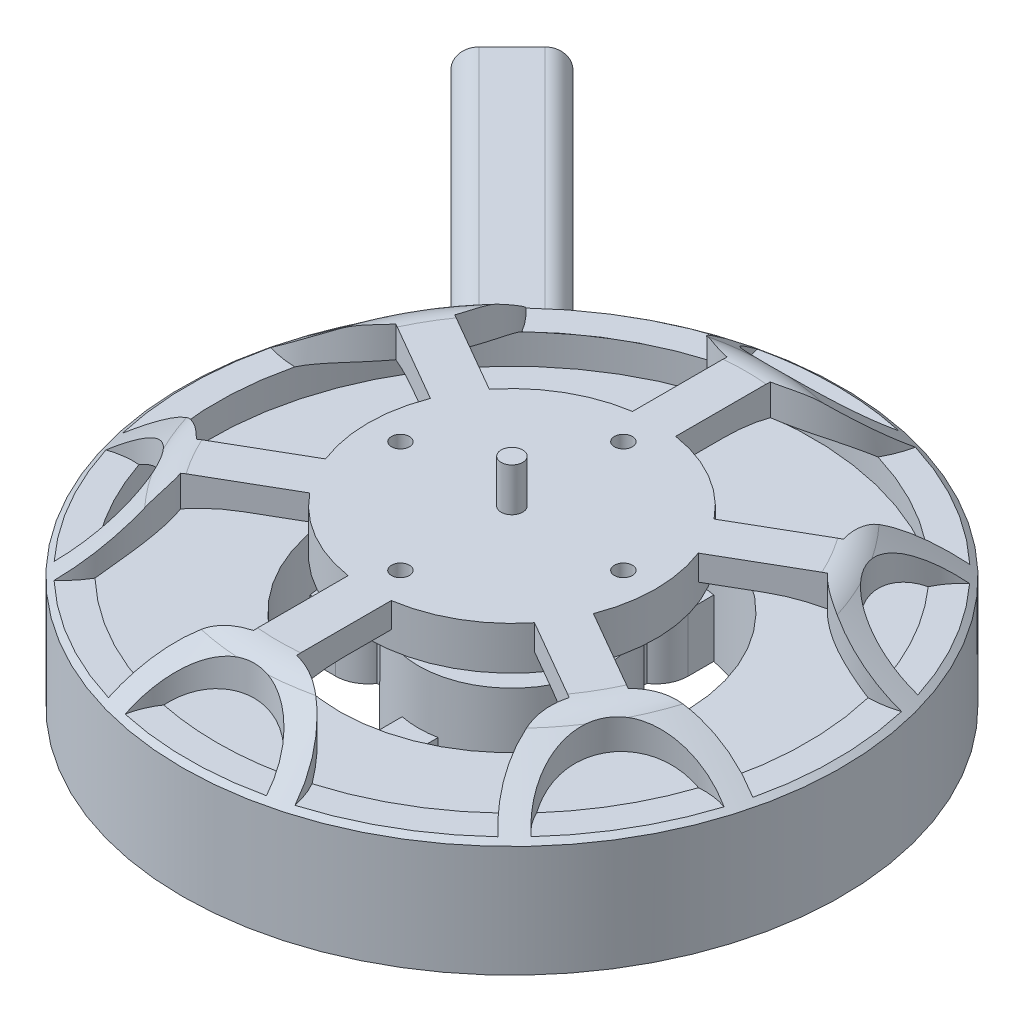
SolidWorks part; units mm, degrees
ref_plane "Front Plane" through (0, 0, 0) normal (0, 0, 1) x (1, 0, 0)
ref_plane "Top Plane" through (0, 0, 0) normal (0, 1, 0) x (1, 0, 0)
ref_plane "Right Plane" through (0, 0, 0) normal (1, 0, 0) x (0, 0, -1)
ref_axis "Axis1" through (0, 40.089, 0) along (0, -1, 0)
sketch "Sketch1" plane through (0, 0, 0) normal (0, 0, 1) x (1, 0, 0)
  line L0 (0, 0) -> (9.65, 0)
  line L1 (9.65, 0) -> (9.65, 3.93)
  line L2 (9.65, 3.93) -> (27.5, 3.93)
  line L3 (27.5, 3.93) -> (45.83, 8.08)
  line L4 (45.83, 8.08) -> (45.83, 23.58)
  line L5 (45.83, 23.58) -> (36.1322, 30.9557)
  line L6 (32.5, 32.18) -> (1.5, 32.18)
  line L7 (1.5, 32.18) -> (1.5, 38.18)
  line L8 (1.5, 38.18) -> (0, 38.18)
  line L9 (0, 38.18) -> (0, 0) construction
  line L10 (0, 0) -> (0, 38.18)
  arc A0 (36.1322, 30.9557) -> (32.5, 32.18) centre (32.5, 26.18) ccw
  dimension "D10" = 6
  dimension "D1" = 3
  dimension "D2" = 6
  dimension "D3" = 28.25
  dimension "D4" = 3.93
  dimension "D5" = 19.3
  dimension "D6" = 4.15
  dimension "D7" = 91.66
  dimension "D8" = 55
  dimension "D9" = 65
  dimension "D11" = 15.5
revolve "Revolve1" add sketch "Sketch1" angle 360 about L9
sketch "Sketch2" plane through (0, 3.93, 0) normal (0, -1, 0) x (1, 0, 0)
  line L0 (0, 0) -> (0, 27.5) construction
  line L1 (2.5, 12.7574) -> (2.5, 16.2583)
  line L2 (4.5, 20) -> (4.5, 23.5744)
  line L3 (0, 0) -> (16.9706, 16.9706) construction
  line L4 (20, 4.5) -> (23.5744, 4.5)
  line L5 (12.7574, 2.5) -> (16.2583, 2.5)
  line L6 (20, -4.5) -> (23.5744, -4.5)
  line L7 (4.5, -20) -> (4.5, -23.5744)
  line L8 (2.5, -12.7574) -> (2.5, -16.2583)
  line L9 (12.7574, -2.5) -> (16.2583, -2.5)
  line L10 (-4.5, -20) -> (-4.5, -23.5744)
  line L11 (-20, -4.5) -> (-23.5744, -4.5)
  line L12 (-12.7574, -2.5) -> (-16.2583, -2.5)
  line L13 (-2.5, -12.7574) -> (-2.5, -16.2583)
  line L14 (-20, 4.5) -> (-23.5744, 4.5)
  line L15 (-4.5, 20) -> (-4.5, 23.5744)
  line L16 (-2.5, 12.7574) -> (-2.5, 16.2583)
  line L17 (-12.7574, 2.5) -> (-16.2583, 2.5)
  arc A0 (4.5, 23.5744) -> (23.5744, 4.5) centre (0, 0) cw
  arc A1 (4.5, 20) -> (2.5, 16.2583) centre (0, 20) cw
  arc A2 (2.5, 12.7574) -> (12.7574, 2.5) centre (0, 0) cw
  circle A3 centre (0, 0) radius 27.5 construction
  arc A4 (20, 4.5) -> (16.2583, 2.5) centre (20, 0) ccw
  arc A5 (20, -4.5) -> (16.2583, -2.5) centre (20, 0) cw
  arc A6 (23.5744, -4.5) -> (4.5, -23.5744) centre (0, 0) cw
  arc A7 (4.5, -20) -> (2.5, -16.2583) centre (0, -20) ccw
  arc A8 (12.7574, -2.5) -> (2.5, -12.7574) centre (0, 0) cw
  arc A9 (-4.5, -20) -> (-2.5, -16.2583) centre (0, -20) cw
  arc A10 (-4.5, -23.5744) -> (-23.5744, -4.5) centre (0, 0) cw
  arc A11 (-20, -4.5) -> (-16.2583, -2.5) centre (-20, 0) ccw
  arc A12 (-2.5, -12.7574) -> (-12.7574, -2.5) centre (0, 0) cw
  arc A13 (-20, 4.5) -> (-16.2583, 2.5) centre (-20, 0) cw
  arc A14 (-23.5744, 4.5) -> (-4.5, 23.5744) centre (0, 0) cw
  arc A15 (-4.5, 20) -> (-2.5, 16.2583) centre (0, 20) ccw
  arc A16 (-12.7574, 2.5) -> (-2.5, 12.7574) centre (0, 0) cw
  point P4 (0, 20)
  point P51 (0, 0)
  dimension "D2" = 13
  dimension "D5" = 24
  dimension "D1" = 20
  dimension "D3" = 5
  dimension "D4" = 9
  dimension "D6" = 45
  dimension "D7" = 4
hole_wizard "M4x0.7 Tapped Hole1" positions "3DSketch1" profile "Sketch4" tap size "M4x0.7" standard "ANSI Metric"
sketch3d "3DSketch1"
  point P0 (-20, 3.93, 0)
  point P3 (0, 3.93, 20)
  point P6 (20, 3.93, 0)
  point P9 (0, 3.93, -20)
sketch "Sketch4" plane through (-20, 3.93, 0) normal (1, 0, 0) x (0, 0, -1)
  line L0 (0, 0) -> (0, 8.9914)
  line L1 (0, 8.9914) -> (1.65, 8)
  line L2 (1.65, 8) -> (1.65, 0)
  line L5 (1.65, 0) -> (0, 0)
  line L10 (0, 8.9914) -> (-1.65, 8) construction
  line L11 (0, -6.35) -> (0, 107.95) construction
  dimension "Tap Drill Dia." = 3.3
  dimension "Tap Drill Depth" = 8
  dimension "Drill Angle" = 118
cosmetic thread "Hole Thread1" parameters "D1"=7.874, "D2"=4
cosmetic thread "Hole Thread2" parameters "D1"=7.874, "D2"=4
cosmetic thread "Hole Thread3" parameters "D1"=7.874, "D2"=4
cosmetic thread "Hole Thread4" parameters "D1"=7.874, "D2"=4
extrude "Cut-Extrude1" cut sketch "Sketch2" against normal blind 8
sketch "Sketch5" plane through (0, 0, 0) normal (0, 0, 1) x (1, 0, 0)
  line L0 (24, 19.43) -> (41.83, 19.43)
  line L1 (-27.5, 3.93) -> (27.5, 3.93) construction
  line L2 (41.83, 19.43) -> (41.83, 23.58)
  line L3 (45.83, 8.08) -> (45.83, 23.58) construction
  line L4 (10, 19.43) -> (13, 19.43)
  line L5 (13, 19.43) -> (13, 11.93)
  line L6 (13, 11.93) -> (24, 11.93)
  line L7 (24, 11.93) -> (24, 19.43)
  line L8 (0, 40.089) -> (0, -1.909) construction
  line L9 (4.5, 11.93) -> (23.5744, 11.93) construction
  line L10 (45.83, 23.58) -> (-45.83, 23.58) construction
  line L11 (20, 28.68) -> (26.6996, 28.68)
  line L12 (32.5, 32.18) -> (-32.5, 32.18) construction
  line L13 (41.83, 23.58) -> (45.83, 20.5378) construction
  line L14 (45.83, 23.58) -> (36.1322, 30.9557) construction
  line L15 (20, 28.68) -> (20, 26.18)
  line L16 (20, 26.18) -> (10, 26.18)
  line L17 (10, 26.18) -> (10, 19.43)
  arc A0 (26.6996, 28.68) -> (41.83, 23.58) centre (26.6996, 3.6861) cw
  dimension "D1" = 15.5
  dimension "D2" = 4
  dimension "D3" = 13
  dimension "D4" = 24
  dimension "D5" = 3.5
  dimension "D6" = 20
  dimension "D7" = 6
  dimension "D8" = 10
revolve "Cut-Revolve3" cut sketch "Sketch5" angle 360 about axis through (0, 40.089, 0) along (0, -1, 0)
sketch "Sketch6" plane through (0, 0, 0) normal (0, 1, 0) x (1, 0, 0)
  line L0 (-3, 19.7737) -> (-3, 32.9241)
  line L1 (3, 19.7737) -> (3, 32.9241)
  line L2 (-3, 19.7737) -> (3, 19.7737) construction
  line L3 (0, 45.83) -> (0, 35.83) construction
  line L4 (15.6245, 12.4849) -> (27.0131, 19.0601)
  line L5 (18.6245, 7.2888) -> (30.0131, 13.864)
  line L6 (15.6245, 12.4849) -> (18.6245, 7.2888) construction
  line L7 (39.6899, 22.915) -> (31.0297, 17.915) construction
  line L8 (18.6245, -7.2888) -> (30.0131, -13.864)
  line L9 (15.6245, -12.4849) -> (27.0131, -19.0601)
  line L10 (18.6245, -7.2888) -> (15.6245, -12.4849) construction
  line L11 (39.6899, -22.915) -> (31.0297, -17.915) construction
  line L12 (3, -19.7737) -> (3, -32.9241)
  line L13 (-3, -19.7737) -> (-3, -32.9241)
  line L14 (3, -19.7737) -> (-3, -19.7737) construction
  line L15 (0, -45.83) -> (0, -35.83) construction
  line L16 (-15.6245, -12.4849) -> (-27.0131, -19.0601)
  line L17 (-18.6245, -7.2888) -> (-30.0131, -13.864)
  line L18 (-15.6245, -12.4849) -> (-18.6245, -7.2888) construction
  line L19 (-39.6899, -22.915) -> (-31.0297, -17.915) construction
  line L20 (-18.6245, 7.2888) -> (-30.0131, 13.864)
  line L21 (-15.6245, 12.4849) -> (-27.0131, 19.0601)
  line L22 (-18.6245, 7.2888) -> (-15.6245, 12.4849) construction
  line L23 (-39.6899, 22.915) -> (-31.0297, 17.915) construction
  line L24 (0, 15.5) -> (15.5, 0) construction
  line L25 (15.5, 0) -> (0, -15.5) construction
  line L26 (0, -15.5) -> (-15.5, 0) construction
  line L27 (-15.5, 0) -> (0, 15.5) construction
  arc A1 (-9.9403, 44.739) -> (9.9403, 44.739) centre (0, 45.83) ccw
  circle A2 centre (0, 0) radius 45.83 construction
  arc A3 (-13.1108, 43.9146) -> (-3, 32.9241) centre (0, 45.83) ccw
  arc A4 (13.1108, 43.9146) -> (3, 32.9241) centre (0, 45.83) cw
  arc A5 (-13.1108, 43.9146) -> (-9.9403, 44.739) centre (0, 0) cw
  arc A6 (9.9403, 44.739) -> (13.1108, 43.9146) centre (0, 0) cw
  arc A7 (33.775, 30.9781) -> (43.7153, 13.7609) centre (39.6899, 22.915) ccw
  arc A8 (31.4758, 33.3116) -> (27.0131, 19.0601) centre (39.6899, 22.915) ccw
  arc A9 (44.5866, 10.603) -> (30.0131, 13.864) centre (39.6899, 22.915) cw
  arc A10 (31.4758, 33.3116) -> (33.775, 30.9781) centre (0, 0) cw
  arc A11 (43.7153, 13.7609) -> (44.5866, 10.603) centre (0, 0) cw
  arc A12 (43.7153, -13.7609) -> (33.775, -30.9781) centre (39.6899, -22.915) ccw
  arc A13 (44.5866, -10.603) -> (30.0131, -13.864) centre (39.6899, -22.915) ccw
  arc A14 (31.4758, -33.3116) -> (27.0131, -19.0601) centre (39.6899, -22.915) cw
  arc A15 (44.5866, -10.603) -> (43.7153, -13.7609) centre (0, 0) cw
  arc A16 (33.775, -30.9781) -> (31.4758, -33.3116) centre (0, 0) cw
  arc A17 (9.9403, -44.739) -> (-9.9403, -44.739) centre (0, -45.83) ccw
  arc A18 (13.1108, -43.9146) -> (3, -32.9241) centre (0, -45.83) ccw
  arc A19 (-13.1108, -43.9146) -> (-3, -32.9241) centre (0, -45.83) cw
  arc A20 (13.1108, -43.9146) -> (9.9403, -44.739) centre (0, 0) cw
  arc A21 (-9.9403, -44.739) -> (-13.1108, -43.9146) centre (0, 0) cw
  arc A22 (-33.775, -30.9781) -> (-43.7153, -13.7609) centre (-39.6899, -22.915) ccw
  arc A23 (-31.4758, -33.3116) -> (-27.0131, -19.0601) centre (-39.6899, -22.915) ccw
  arc A24 (-44.5866, -10.603) -> (-30.0131, -13.864) centre (-39.6899, -22.915) cw
  arc A25 (-31.4758, -33.3116) -> (-33.775, -30.9781) centre (0, 0) cw
  arc A26 (-43.7153, -13.7609) -> (-44.5866, -10.603) centre (0, 0) cw
  arc A27 (-43.7153, 13.7609) -> (-33.775, 30.9781) centre (-39.6899, 22.915) ccw
  arc A28 (-44.5866, 10.603) -> (-30.0131, 13.864) centre (-39.6899, 22.915) ccw
  arc A29 (-31.4758, 33.3116) -> (-27.0131, 19.0601) centre (-39.6899, 22.915) cw
  arc A30 (-44.5866, 10.603) -> (-43.7153, 13.7609) centre (0, 0) cw
  arc A31 (-33.775, 30.9781) -> (-31.4758, 33.3116) centre (0, 0) cw
  arc A32 (3, 19.7737) -> (15.6245, 12.4849) centre (0, 0) cw
  arc A33 (18.6245, 7.2888) -> (18.6245, -7.2888) centre (0, 0) cw
  arc A34 (15.6245, -12.4849) -> (3, -19.7737) centre (0, 0) cw
  arc A35 (-3, -19.7737) -> (-15.6245, -12.4849) centre (0, 0) cw
  arc A36 (-18.6245, -7.2888) -> (-18.6245, 7.2888) centre (0, 0) cw
  arc A37 (-3, 19.7737) -> (-15.6245, 12.4849) centre (0, 0) ccw
  point P0 (0, 19.7737)
  point P17 (0, 15.5)
  point P28 (15.5, 0)
  point P38 (0, -15.5)
  point P68 (0, 0)
  point P69 (-15.5, 0)
  dimension "D1" = 6
  dimension "D3" = 3.25
  dimension "D5" = 20
  dimension "D2" = 6
  dimension "D4" = 10
  dimension "D6" = 15.5
extrude "Cut-Extrude3" cut sketch "Sketch6" against normal blind 8 from surface at 32.18 flip side to cut starting at face at (0, 32.18, 1.5)
hole_wizard "M3x0.5 Tapped Hole1" positions "Sketch8" profile "Sketch10" tap size "M3x0.5" standard "ANSI Metric" end condition up to next
sketch "Sketch8" plane through (0, 32.18, 0) normal (0, 1, 0) x (1, 0, 0)
  point P0 (0, 15.5)
  point P3 (15.5, 0)
  point P6 (0, -15.5)
  point P9 (-15.5, 0)
sketch "Sketch10" plane through (0, 32.18, -15.5) normal (1, 0, 0) x (0, 0, 1)
  line L0 (0, 0) -> (0, 6)
  line L1 (0, 6) -> (1.25, 6)
  line L2 (1.25, 6) -> (1.25, 0)
  line L5 (1.25, 0) -> (0, 0)
  line L11 (0, -6.35) -> (0, 107.95) construction
  dimension "Thru Tap Drill Dia." = 2.5
  dimension "Thru Tap Drill Depth" = 6
cosmetic thread "Hole Thread5" parameters "D2"=3
cosmetic thread "Hole Thread6" parameters "D2"=3
cosmetic thread "Hole Thread7" parameters "D2"=3
cosmetic thread "Hole Thread8" parameters "D2"=3
sketch "Sketch11" plane through (0, 0, 0) normal (0, 1, 0) x (1, 0, 0)
  line L0 (-26.0427, 21.4465) -> (-21.4465, 26.0427) construction
  line L1 (-27.9873, 23.3911) -> (-23.3911, 27.9873)
  line L2 (-24.0982, 19.502) -> (-19.502, 24.0982)
  line L3 (-23.7446, 23.7446) -> (0, 0) construction
  line L4 (-20, 0) -> (0, 20) construction
  line L5 (-27.9873, 19.502) -> (-19.502, 27.9873) construction
  line L6 (-25.6892, 25.6892) -> (-32.4067, 32.4067) construction
  arc A0 (-27.9873, 23.3911) -> (-24.0982, 19.502) centre (-26.0427, 21.4465) ccw
  arc A1 (-19.502, 24.0982) -> (-23.3911, 27.9873) centre (-21.4465, 26.0427) ccw
  arc A2 (3, 19.7737) -> (-3, 19.7737) centre (0, 0) ccw construction
  circle A3 centre (0, 0) radius 45.83 construction
  point P2 (-23.7446, 23.7446)
  dimension "D1" = 12
  dimension "D2" = 5.5
  dimension "D3" = 9.5
extrude "Boss-Extrude1" add sketch "Sketch11" against normal blind 19.05 from offset 12.7
ref_plane "Plane1" through (0, 0, 0) normal (-0.7071, 0, 0.7071) x (0.7071, 0, 0.7071)
sketch "Sketch12" plane through (0, 0, 0) normal (-0.7071, 0, 0.7071) x (0.7071, 0, 0.7071)
  line L0 (-36.33, -6.35) -> (-36.33, 5.962) construction
  line L1 (-49.03, -19.05) -> (-150.63, -19.05)
  arc A0 (-36.33, -6.35) -> (-49.03, -19.05) centre (-49.03, -6.35) cw
  dimension "D1" = 12.7
  dimension "D2" = 101.6
sketch "Sketch13" plane through (0, -6.35, 0) normal (0, -1, 0) x (1, 0, 0)
  line L2 (-27.9873, -23.3911) -> (-23.3911, -27.9873)
  line L3 (-19.502, -24.0982) -> (-24.0982, -19.502)
  line L4 (-27.9873, -23.3911) -> (-23.3911, -27.9873)
  line L5 (-19.502, -24.0982) -> (-24.0982, -19.502)
  arc A2 (-24.0982, -19.502) -> (-27.9873, -23.3911) centre (-26.0427, -21.4465) ccw
  arc A3 (-23.3911, -27.9873) -> (-19.502, -24.0982) centre (-21.4465, -26.0427) ccw
  arc A4 (-24.0982, -19.502) -> (-27.9873, -23.3911) centre (-26.0427, -21.4465) ccw
  arc A5 (-23.3911, -27.9873) -> (-19.502, -24.0982) centre (-21.4465, -26.0427) ccw
  dimension "D1" = 0
sweep "Sweep1" add profiles "Sketch13" path "Sketch12"
equation "\"INTERIOR_STATOR_BORE_OD\"= 48MM"
equation "\"INTERIOR_STATOR_BORE_ID\"= 26mm"
equation "\"D5@Sketch2\"=\"INTERIOR_STATOR_BORE_OD\"/2"
equation "\"D2@Sketch2\"=\"INTERIOR_STATOR_BORE_ID\"/2"
equation "\"D3@Sketch5\"=\"INTERIOR_STATOR_BORE_ID\"/2"
equation "\"D4@Sketch5\"=\"INTERIOR_STATOR_BORE_OD\"/2"
